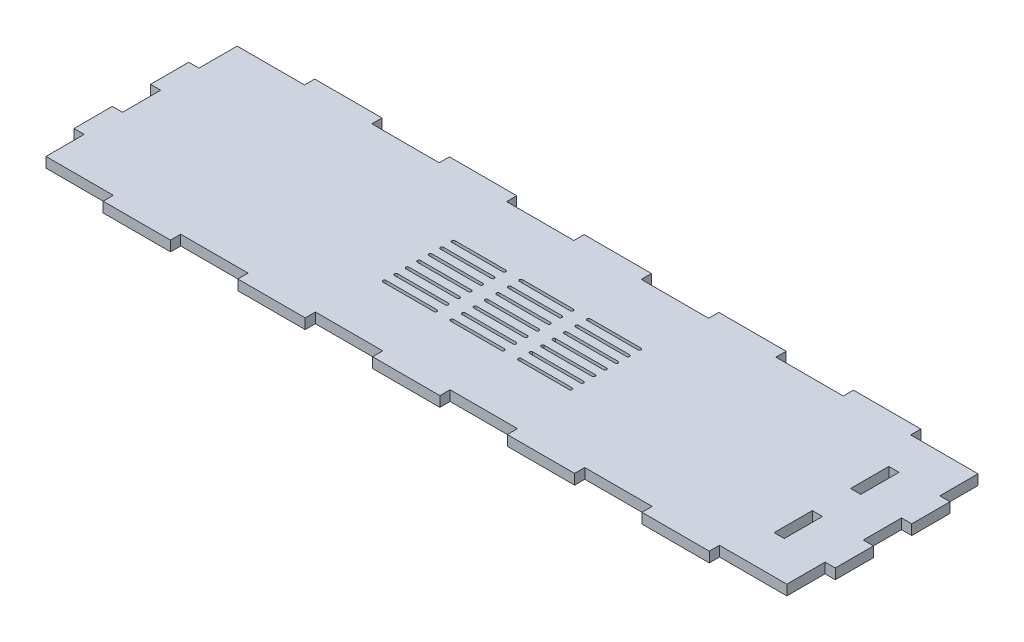
SolidWorks part; units mm, degrees
ref_plane "Front Plane" through (0, 0, 0) normal (0, 0, 1) x (1, 0, 0)
ref_plane "Top Plane" through (0, 0, 0) normal (0, 1, 0) x (1, 0, 0)
ref_plane "Right Plane" through (0, 0, 0) normal (1, 0, 0) x (0, 0, -1)
sketch "Sketch1" plane through (0, 0, 0) normal (0, 1, 0) x (1, 0, 0)
  line L1 (-218, -56.25) -> (218, -56.25)
  line L2 (-218, -56.25) -> (-218, 56.25)
  line L3 (-218, 56.25) -> (218, 56.25)
  line L4 (218, -56.25) -> (218, 56.25)
  line L5 (-218, -56.25) -> (218, 56.25) construction
  line L6 (-218, 56.25) -> (218, -56.25) construction
  point P0 (0, 0)
  dimension "D1" = 436
  dimension "D2" = 112.5
extrude "Boss-Extrude1" add sketch "Sketch1" along normal blind 6
sketch "Sketch2" plane through (-218, 0, 0) normal (-1, 0, 0) x (0, 0, 1)
  line L0 (-56.25, 6) -> (56.25, 6) construction
  line L1 (-56.25, 0) -> (-33.75, 0) construction
  line L2 (-56.25, 0) -> (-56.25, 6)
  line L3 (-56.25, 6) -> (-33.75, 6)
  line L4 (-33.75, 0) -> (-33.75, 6)
  line L5 (-56.25, 0) -> (56.25, 0) construction
  line L6 (-33.75, 6) -> (-11.25, 6)
  line L7 (-33.75, 6) -> (-33.75, 0)
  line L8 (-33.75, 0) -> (-11.25, 0)
  line L9 (-11.25, 6) -> (-11.25, 0)
  line L11 (-11.25, 0) -> (11.25, 0) construction
  line L12 (-11.25, 0) -> (-11.25, 6)
  line L13 (-11.25, 6) -> (11.25, 6)
  line L14 (11.25, 0) -> (11.25, 6)
  line L15 (11.25, 6) -> (33.75, 6)
  line L16 (11.25, 6) -> (11.25, 0)
  line L17 (11.25, 0) -> (33.75, 0)
  line L18 (33.75, 6) -> (33.75, 0)
  line L19 (33.75, 0) -> (56.25, 0) construction
  line L20 (33.75, 0) -> (33.75, 6)
  line L21 (33.75, 6) -> (56.25, 6)
  line L22 (56.25, 0) -> (56.25, 6)
  line M9 (-56.25, 0) -> (56.25, 0)
  line M11 (56.25, 6) -> (-56.25, 6)
extrude "Boss-Extrude2" add sketch "Sketch2" along normal blind 6 contours L9 L4 M11 M9 | L18 L14 M11 M9
mirror "Mirror1" about plane through (0, 0, 0) normal (1, 0, 0) of "Boss-Extrude2"
sketch "Sketch3" plane through (0, 0, -56.25) normal (0, 0, -1) x (-1, 0, 0)
  line L0 (-218, 0) -> (218, 0) construction
  line L1 (218, 6) -> (178.3636, 6)
  line L2 (218, 6) -> (218, 0)
  line L3 (218, 0) -> (178.3636, 0)
  line L4 (178.3636, 6) -> (178.3636, 0)
  line L5 (-218, 6) -> (218, 6) construction
  line L6 (178.3636, 0) -> (138.7273, 0)
  line L7 (178.3636, 0) -> (178.3636, 6)
  line L8 (178.3636, 6) -> (138.7273, 6)
  line L9 (138.7273, 0) -> (138.7273, 6)
  line L11 (138.7273, 6) -> (99.0909, 6)
  line L12 (138.7273, 6) -> (138.7273, 0)
  line L13 (138.7273, 0) -> (99.0909, 0)
  line L14 (99.0909, 6) -> (99.0909, 0)
  line L15 (99.0909, 0) -> (59.4545, 0)
  line L16 (99.0909, 0) -> (99.0909, 6)
  line L17 (99.0909, 6) -> (59.4545, 6)
  line L18 (59.4545, 0) -> (59.4545, 6)
  line L19 (59.4545, 6) -> (19.8182, 6)
  line L20 (59.4545, 6) -> (59.4545, 0)
  line L21 (59.4545, 0) -> (19.8182, 0)
  line L22 (19.8182, 6) -> (19.8182, 0)
  line L23 (19.8182, 0) -> (-19.8182, 0)
  line L24 (19.8182, 0) -> (19.8182, 6)
  line L25 (19.8182, 6) -> (-19.8182, 6)
  line L26 (-19.8182, 0) -> (-19.8182, 6)
  line L27 (-19.8182, 6) -> (-59.4545, 6)
  line L28 (-19.8182, 6) -> (-19.8182, 0)
  line L29 (-19.8182, 0) -> (-59.4545, 0)
  line L30 (-59.4545, 6) -> (-59.4545, 0)
  line L31 (-59.4545, 0) -> (-99.0909, 0)
  line L32 (-59.4545, 0) -> (-59.4545, 6)
  line L33 (-59.4545, 6) -> (-99.0909, 6)
  line L34 (-99.0909, 0) -> (-99.0909, 6)
  line L35 (-99.0909, 6) -> (-138.7273, 6)
  line L36 (-99.0909, 6) -> (-99.0909, 0)
  line L37 (-99.0909, 0) -> (-138.7273, 0)
  line L38 (-138.7273, 6) -> (-138.7273, 0)
  line L39 (-138.7273, 0) -> (-178.3636, 0)
  line L40 (-138.7273, 0) -> (-138.7273, 6)
  line L41 (-138.7273, 6) -> (-178.3636, 6)
  line L42 (-178.3636, 0) -> (-178.3636, 6)
  line L43 (-178.3636, 6) -> (-218, 6)
  line L44 (-178.3636, 6) -> (-178.3636, 0)
  line L45 (-178.3636, 0) -> (-218, 0)
  line L46 (-218, 6) -> (-218, 0)
  line M30 (-218, 0) -> (218, 0)
  line M32 (218, 6) -> (-218, 6)
extrude "Boss-Extrude3" add sketch "Sketch3" along normal blind 6 contours L9 L4 M30 M32 | L18 L14 M30 M32 | L26 L22 M30 M32 | L34 L30 M30 M32 | L42 L38 M30 M32
mirror "Mirror2" of "Boss-Extrude3"
sketch "Sketch4" plane through (0, 0, 0) normal (0, -1, 0) x (1, 0, 0)
  line L1 (188, 33.75) -> (194, 33.75)
  line L2 (188, 33.75) -> (188, 11.25)
  line L3 (188, 11.25) -> (194, 11.25)
  line L4 (194, 33.75) -> (194, 11.25)
  line L5 (194, -11.25) -> (188, -11.25)
  line L6 (194, -11.25) -> (194, -33.75)
  line L7 (194, -33.75) -> (188, -33.75)
  line L8 (188, -11.25) -> (188, -33.75)
extrude "Cut-Extrude1" cut sketch "Sketch4" against normal blind 6
sketch "Sketch5" plane through (0, 6, 0) normal (0, 1, 0) x (1, 0, 0)
  line L0 (0, 0) -> (0, 20.25) construction
  line L3 (-54.8, 13.5) -> (-24.8, 13.5) construction
  line L4 (0, 20.25) -> (-39.8, 20.25) construction
  line L5 (-19.8182, 56.25) -> (-59.4545, 56.25) construction
  line L6 (-54.8, 20.25) -> (-24.8, 20.25) construction
  line L7 (-54.8, 21.15) -> (-24.8, 21.15)
  line L8 (-54.8, 19.35) -> (-24.8, 19.35)
  line L9 (-15, 20.25) -> (15, 20.25) construction
  line L10 (-15, 21.15) -> (15, 21.15)
  line L11 (-15, 19.35) -> (15, 19.35)
  line L12 (54.8, 20.25) -> (24.8, 20.25) construction
  line L13 (54.8, 21.15) -> (24.8, 21.15)
  line L14 (54.8, 19.35) -> (24.8, 19.35)
  line L15 (-54.8, 14.4) -> (-24.8, 14.4)
  line L16 (-54.8, 12.6) -> (-24.8, 12.6)
  line L17 (-15, 13.5) -> (15, 13.5) construction
  line L18 (-15, 14.4) -> (15, 14.4)
  line L19 (-15, 12.6) -> (15, 12.6)
  line L20 (54.8, 13.5) -> (24.8, 13.5) construction
  line L21 (54.8, 14.4) -> (24.8, 14.4)
  line L22 (54.8, 12.6) -> (24.8, 12.6)
  line L23 (-54.8, 6.75) -> (-24.8, 6.75) construction
  line L24 (-54.8, 7.65) -> (-24.8, 7.65)
  line L25 (-54.8, 5.85) -> (-24.8, 5.85)
  line L26 (-15, 6.75) -> (15, 6.75) construction
  line L27 (-15, 7.65) -> (15, 7.65)
  line L28 (-15, 5.85) -> (15, 5.85)
  line L29 (54.8, 6.75) -> (24.8, 6.75) construction
  line L30 (54.8, 7.65) -> (24.8, 7.65)
  line L31 (54.8, 5.85) -> (24.8, 5.85)
  line L32 (-54.8, 0) -> (-24.8, 0) construction
  line L33 (-54.8, 0.9) -> (-24.8, 0.9)
  line L34 (-54.8, -0.9) -> (-24.8, -0.9)
  line L35 (-15, 0) -> (15, 0) construction
  line L36 (-15, 0.9) -> (15, 0.9)
  line L37 (-15, -0.9) -> (15, -0.9)
  line L38 (54.8, 0) -> (24.8, 0) construction
  line L39 (54.8, 0.9) -> (24.8, 0.9)
  line L40 (54.8, -0.9) -> (24.8, -0.9)
  line L41 (-54.8, -6.75) -> (-24.8, -6.75) construction
  line L42 (-54.8, -5.85) -> (-24.8, -5.85)
  line L43 (-54.8, -7.65) -> (-24.8, -7.65)
  line L44 (-15, -6.75) -> (15, -6.75) construction
  line L45 (-15, -5.85) -> (15, -5.85)
  line L46 (-15, -7.65) -> (15, -7.65)
  line L47 (54.8, -6.75) -> (24.8, -6.75) construction
  line L48 (54.8, -5.85) -> (24.8, -5.85)
  line L49 (54.8, -7.65) -> (24.8, -7.65)
  line L50 (-54.8, -13.5) -> (-24.8, -13.5) construction
  line L51 (-54.8, -12.6) -> (-24.8, -12.6)
  line L52 (-54.8, -14.4) -> (-24.8, -14.4)
  line L53 (-15, -13.5) -> (15, -13.5) construction
  line L54 (-15, -12.6) -> (15, -12.6)
  line L55 (-15, -14.4) -> (15, -14.4)
  line L56 (54.8, -13.5) -> (24.8, -13.5) construction
  line L57 (54.8, -12.6) -> (24.8, -12.6)
  line L58 (54.8, -14.4) -> (24.8, -14.4)
  line L59 (-54.8, -20.25) -> (-24.8, -20.25) construction
  line L60 (-54.8, -19.35) -> (-24.8, -19.35)
  line L61 (-54.8, -21.15) -> (-24.8, -21.15)
  line L62 (-15, -20.25) -> (15, -20.25) construction
  line L63 (-15, -19.35) -> (15, -19.35)
  line L64 (-15, -21.15) -> (15, -21.15)
  line L65 (54.8, -20.25) -> (24.8, -20.25) construction
  line L66 (54.8, -19.35) -> (24.8, -19.35)
  line L67 (54.8, -21.15) -> (24.8, -21.15)
  arc A2 (-54.8, 21.15) -> (-54.8, 19.35) centre (-54.8, 20.25) ccw
  arc A3 (-24.8, 19.35) -> (-24.8, 21.15) centre (-24.8, 20.25) ccw
  arc A4 (-15, 21.15) -> (-15, 19.35) centre (-15, 20.25) ccw
  arc A5 (15, 19.35) -> (15, 21.15) centre (15, 20.25) ccw
  arc A6 (54.8, 21.15) -> (54.8, 19.35) centre (54.8, 20.25) cw
  arc A7 (24.8, 19.35) -> (24.8, 21.15) centre (24.8, 20.25) cw
  arc A8 (-54.8, 14.4) -> (-54.8, 12.6) centre (-54.8, 13.5) ccw
  arc A9 (-24.8, 12.6) -> (-24.8, 14.4) centre (-24.8, 13.5) ccw
  arc A10 (-15, 14.4) -> (-15, 12.6) centre (-15, 13.5) ccw
  arc A11 (15, 12.6) -> (15, 14.4) centre (15, 13.5) ccw
  arc A12 (54.8, 14.4) -> (54.8, 12.6) centre (54.8, 13.5) cw
  arc A13 (24.8, 12.6) -> (24.8, 14.4) centre (24.8, 13.5) cw
  arc A14 (-54.8, 7.65) -> (-54.8, 5.85) centre (-54.8, 6.75) ccw
  arc A15 (-24.8, 5.85) -> (-24.8, 7.65) centre (-24.8, 6.75) ccw
  arc A16 (-15, 7.65) -> (-15, 5.85) centre (-15, 6.75) ccw
  arc A17 (15, 5.85) -> (15, 7.65) centre (15, 6.75) ccw
  arc A18 (54.8, 7.65) -> (54.8, 5.85) centre (54.8, 6.75) cw
  arc A19 (24.8, 5.85) -> (24.8, 7.65) centre (24.8, 6.75) cw
  arc A20 (-54.8, 0.9) -> (-54.8, -0.9) centre (-54.8, 0) ccw
  arc A21 (-24.8, -0.9) -> (-24.8, 0.9) centre (-24.8, 0) ccw
  arc A22 (-15, 0.9) -> (-15, -0.9) centre (-15, 0) ccw
  arc A23 (15, -0.9) -> (15, 0.9) centre (15, 0) ccw
  arc A24 (54.8, 0.9) -> (54.8, -0.9) centre (54.8, 0) cw
  arc A25 (24.8, -0.9) -> (24.8, 0.9) centre (24.8, 0) cw
  arc A26 (-54.8, -5.85) -> (-54.8, -7.65) centre (-54.8, -6.75) ccw
  arc A27 (-24.8, -7.65) -> (-24.8, -5.85) centre (-24.8, -6.75) ccw
  arc A28 (-15, -5.85) -> (-15, -7.65) centre (-15, -6.75) ccw
  arc A29 (15, -7.65) -> (15, -5.85) centre (15, -6.75) ccw
  arc A30 (54.8, -5.85) -> (54.8, -7.65) centre (54.8, -6.75) cw
  arc A31 (24.8, -7.65) -> (24.8, -5.85) centre (24.8, -6.75) cw
  arc A32 (-54.8, -12.6) -> (-54.8, -14.4) centre (-54.8, -13.5) ccw
  arc A33 (-24.8, -14.4) -> (-24.8, -12.6) centre (-24.8, -13.5) ccw
  arc A34 (-15, -12.6) -> (-15, -14.4) centre (-15, -13.5) ccw
  arc A35 (15, -14.4) -> (15, -12.6) centre (15, -13.5) ccw
  arc A36 (54.8, -12.6) -> (54.8, -14.4) centre (54.8, -13.5) cw
  arc A37 (24.8, -14.4) -> (24.8, -12.6) centre (24.8, -13.5) cw
  arc A38 (-54.8, -19.35) -> (-54.8, -21.15) centre (-54.8, -20.25) ccw
  arc A39 (-24.8, -21.15) -> (-24.8, -19.35) centre (-24.8, -20.25) ccw
  arc A40 (-15, -19.35) -> (-15, -21.15) centre (-15, -20.25) ccw
  arc A41 (15, -21.15) -> (15, -19.35) centre (15, -20.25) ccw
  arc A42 (54.8, -19.35) -> (54.8, -21.15) centre (54.8, -20.25) cw
  arc A43 (24.8, -21.15) -> (24.8, -19.35) centre (24.8, -20.25) cw
  point P8 (-39.8, 20.25)
  point P16 (0, 20.25)
  point P21 (-23.9, 20.25)
  point P22 (-15.9, 20.25)
  point P24 (0, 0)
  point P27 (39.8, 20.25)
  point P32 (-39.8, 13.5)
  point P39 (0, 13.5)
  point P46 (39.8, 13.5)
  point P53 (-39.8, 6.75)
  point P60 (0, 6.75)
  point P67 (39.8, 6.75)
  point P74 (-39.8, 0)
  point P81 (0, 0)
  point P88 (39.8, 0)
  point P95 (-39.8, -6.75)
  point P102 (0, -6.75)
  point P109 (39.8, -6.75)
  point P116 (-39.8, -13.5)
  point P123 (0, -13.5)
  point P130 (39.8, -13.5)
  point P137 (-39.8, -20.25)
  point P144 (0, -20.25)
  point P151 (39.8, -20.25)
  point P156 (0, 0)
  dimension "D1" = 36
  dimension "D2" = 1.8
  dimension "D3" = 8
  dimension "D4" = 30
  dimension "D6" = 4.95
  dimension "D5" = 7
extrude "Cut-Extrude2" cut sketch "Sketch5" against normal through all
